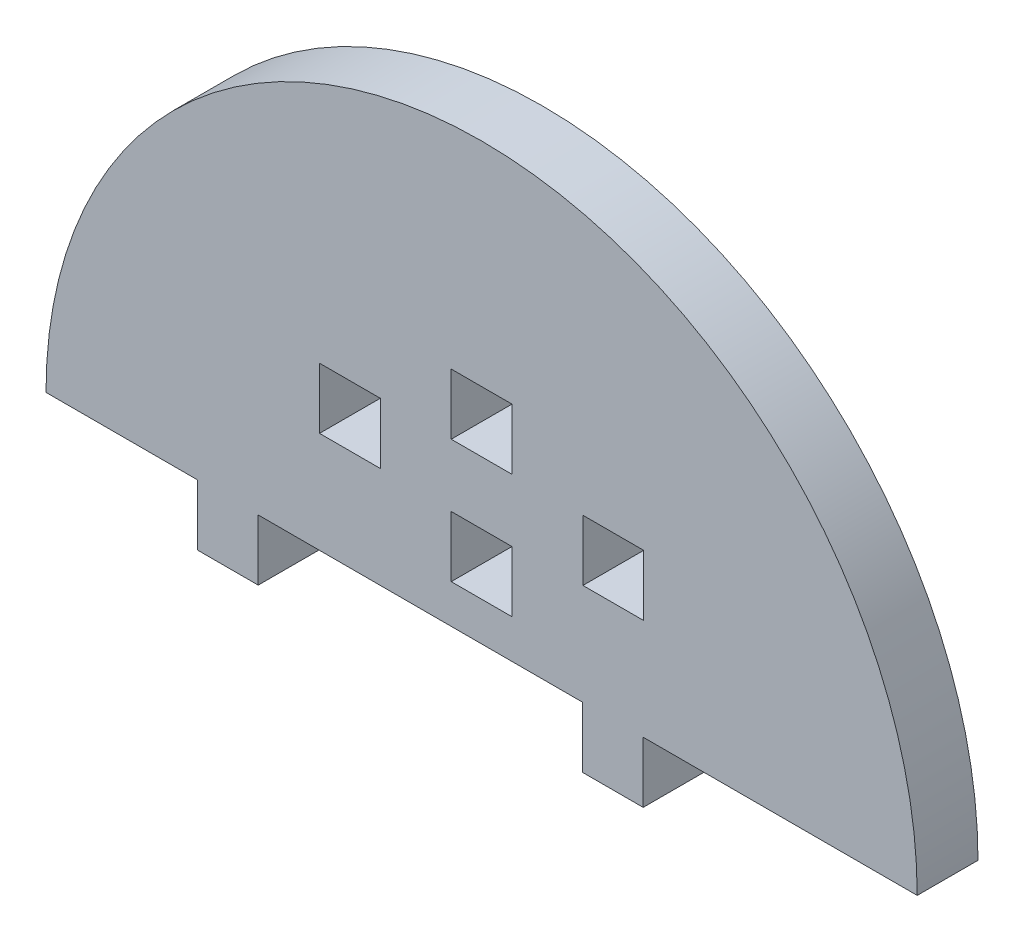
SolidWorks part; units mm, degrees
ref_plane "Front Plane" through (0, 0, 0) normal (0, 0, 1) x (1, 0, 0)
ref_plane "Top Plane" through (0, 0, 0) normal (0, 1, 0) x (1, 0, 0)
ref_plane "Right Plane" through (0, 0, 0) normal (1, 0, 0) x (0, 0, -1)
sketch "Model" plane through (0, 0, 0) normal (0, 0, 1) x (1, 0, 0)
  line L0 (3473.9443, 1077.7489) -> (3479.9443, 1077.7489)
  line L1 (3479.9443, 1077.7489) -> (3479.9443, 1071.7489)
  line L2 (3479.9443, 1071.7489) -> (3473.9443, 1071.7489)
  line L3 (3473.9443, 1071.7489) -> (3473.9443, 1077.7489)
  line L4 (3453.9443, 1077.7489) -> (3447.9443, 1077.7489)
  line L5 (3447.9443, 1077.7489) -> (3447.9443, 1071.7489)
  line L6 (3447.9443, 1071.7489) -> (3453.9443, 1071.7489)
  line L7 (3453.9443, 1071.7489) -> (3453.9443, 1077.7489)
  line L8 (3460.9443, 1083.7489) -> (3466.9443, 1083.7489)
  line L9 (3466.9443, 1083.7489) -> (3466.9443, 1077.7489)
  line L10 (3466.9443, 1077.7489) -> (3460.9443, 1077.7489)
  line L11 (3460.9443, 1077.7489) -> (3460.9443, 1083.7489)
  line L12 (3460.9443, 1065.5734) -> (3466.9443, 1065.5734)
  line L13 (3466.9443, 1065.5734) -> (3466.9443, 1071.5734)
  line L14 (3466.9443, 1071.5734) -> (3460.9443, 1071.5734)
  line L15 (3460.9443, 1071.5734) -> (3460.9443, 1065.5734)
  line L16 (3463.893, 1061.7489) -> (3473.893, 1061.7489)
  line L17 (3473.893, 1061.7489) -> (3473.893, 1055.7489)
  line L18 (3473.893, 1055.7489) -> (3479.893, 1055.7489)
  line L19 (3479.893, 1055.7489) -> (3479.893, 1061.7489)
  line L20 (3479.893, 1061.7489) -> (3491.893, 1061.7489)
  line L21 (3491.893, 1061.7489) -> (3506.9443, 1061.7489)
  line L22 (3463.893, 1061.7489) -> (3441.893, 1061.7489)
  line L23 (3441.893, 1061.7489) -> (3441.893, 1055.7489)
  line L24 (3441.893, 1055.7489) -> (3435.893, 1055.7489)
  line L25 (3435.893, 1055.7489) -> (3435.893, 1061.7489)
  line L26 (3435.893, 1061.7489) -> (3420.9443, 1061.7489)
  arc A0 (3506.9443, 1061.7489) -> (3420.9443, 1061.7489) centre (3463.9443, 1061.7489) ccw
extrude "Boss-Extrude1" add sketch "Model" along normal blind 6 contours L6 L7 L4 L5 | L11 L10 L9 L8 | L14 L15 L12 L13 | L3 L2 L1 L0 | A0 L26 L25 L24 L23 L22 L16 L17 L18 L19 L20 L21
